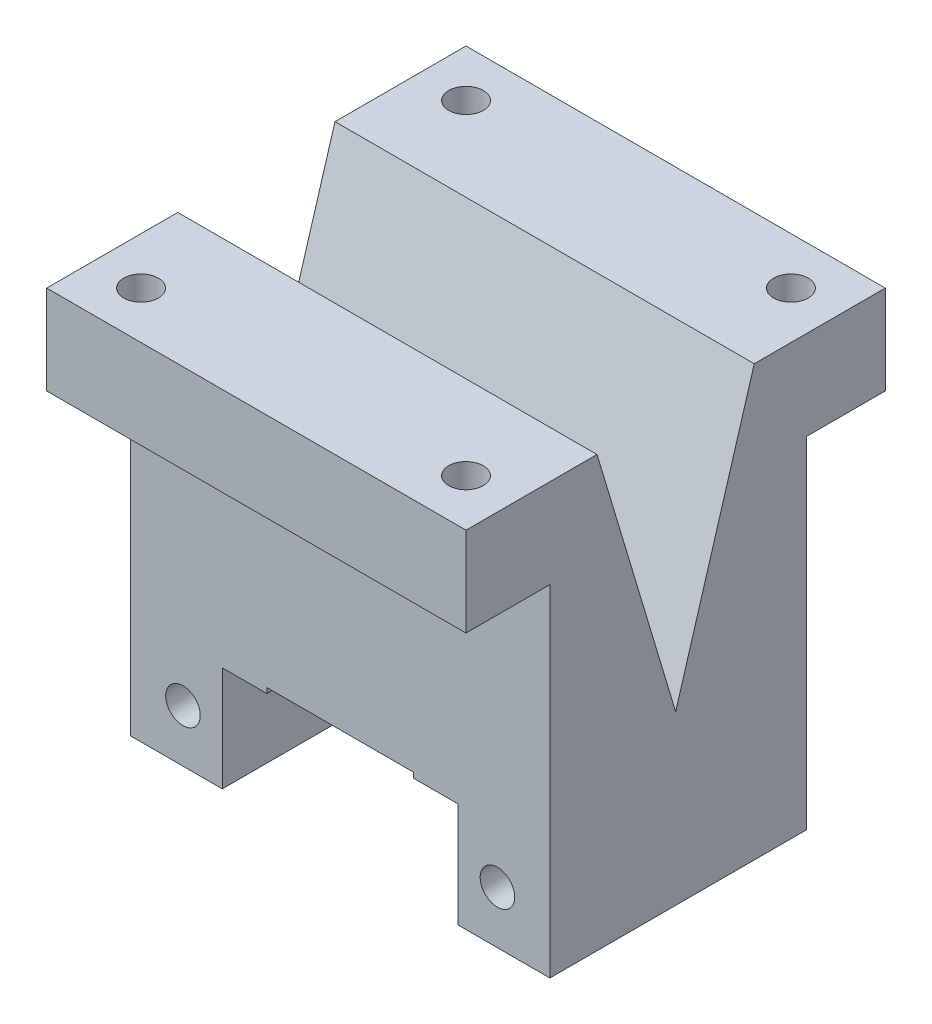
SolidWorks part; units mm, degrees
ref_plane "Front Plane" through (0, 0, 0) normal (0, 0, 1) x (1, 0, 0)
ref_plane "Top Plane" through (0, 0, 0) normal (0, 1, 0) x (1, 0, 0)
ref_plane "Right Plane" through (0, 0, 0) normal (1, 0, 0) x (0, 0, -1)
sketch "Sketch1" plane through (0, 0, 0) normal (0, 1, 0) x (1, 0, 0)
  line L1 (20, 20) -> (-20, 20)
  line L2 (20, 20) -> (20, -20)
  line L3 (20, -20) -> (-20, -20)
  line L4 (-20, 20) -> (-20, -20)
  line L5 (0, -20) -> (0, 20) construction
  line L6 (20, 0) -> (-20, 0) construction
  point P0 (0, 0)
extrude "Boss-Extrude1" add sketch "Sketch1" against normal blind 41
hole_wizard "M4x0.7 Tapped Hole1" positions "Sketch2" profile "Sketch3" tap size "M4x0.7" standard "ANSI Metric" end condition through all
sketch "Sketch2" plane through (0, 0, 0) normal (0, 1, 0) x (1, 0, 0)
  line L1 (-15.5, -15.5) -> (15.5, -15.5)
  line L2 (-15.5, -15.5) -> (-15.5, 15.5)
  line L3 (-15.5, 15.5) -> (15.5, 15.5)
  line L4 (15.5, -15.5) -> (15.5, 15.5)
  line L5 (15.5, 0) -> (0, 0) construction
  line L6 (0, 0) -> (0, -15.5) construction
  point P2 (-15.5, 15.5)
  point P4 (15.5, 15.5)
  point P6 (15.5, -15.5)
  point P8 (-15.5, -15.5)
  dimension "D1" = 31
  dimension "D2" = 31
sketch "Sketch3" plane through (-15.5, 0, -15.5) normal (1, 0, 0) x (0, 0, 1)
  line L0 (0, 0) -> (0, 41)
  line L1 (0, 41) -> (1.65, 41)
  line L2 (1.65, 41) -> (1.65, 0)
  line L5 (1.65, 0) -> (0, 0)
  line L11 (0, -6.35) -> (0, 107.95) construction
  dimension "Thread Major Dia." = 3.3
  dimension "Thru Tap Drill Depth" = 41
sketch "Sketch10" plane through (0, 0, 0) normal (0, 1, 0) x (1, 0, 0)
  line L0 (20, -20) -> (20, 20) construction
  line L1 (-20, -20) -> (20, -20)
  line L2 (-20, -20) -> (-20, 0)
  line L3 (-20, 0) -> (20, 0)
  line L4 (20, -20) -> (20, 0)
sketch "Sketch11" plane through (0, 0, 0) normal (0, 0, 1) x (1, 0, 0)
  line L0 (0, 0) -> (0, -32.5) construction
  line L1 (0, -32.5) -> (11.25, -32.5)
  line L2 (0, -32.5) -> (0, -39.5)
  line L3 (0, -39.5) -> (11.25, -39.5)
  line L4 (11.25, -32.5) -> (11.25, -39.5)
  point P5 (0, 0)
  point P6 (0, 0)
  dimension "D1" = 32.5
  dimension "D2" = 7
  dimension "D3" = 22.5
revolve "Cut-Revolve2" cut sketch "Sketch11" angle 360 about L0
sketch "Sketch12" plane through (0, -41, 0) normal (0, -1, 0) x (1, 0, 0)
  circle A0 centre (0, 0) radius 10
  point P2 (0, 0)
  dimension "D1" = 20
extrude "Cut-Extrude5" cut sketch "Sketch12" against normal up to next
hole_wizard "M4x0.7 Tapped Hole2" positions "Sketch13" profile "Sketch14" tap size "M4x0.7" standard "ANSI Metric" end condition through all
sketch "Sketch13" plane through (0, 0, -20) normal (0, 0, -1) x (-1, 0, 0)
  line L0 (-15, -36) -> (15, -36) construction
  line L3 (0, -36) -> (0, 0) construction
  line L9 (20, -41) -> (-20, -41) construction
  point P8 (15, -36)
  point P10 (-15, -36)
  point P34 (0, 0)
  point P35 (0, 0)
  point P36 (0, 0)
  point P38 (0, 0)
  dimension "D1" = 30
  dimension "D2" = 5
sketch "Sketch14" plane through (-15, -36, -20) normal (1, 0, 0) x (0, 1, 0)
  line L0 (0, 0) -> (0, 40)
  line L1 (0, 40) -> (1.65, 40)
  line L2 (1.65, 40) -> (1.65, 0)
  line L5 (1.65, 0) -> (0, 0)
  line L11 (0, -6.35) -> (0, 107.95) construction
  dimension "Thru Tap Drill Dia." = 3.3
  dimension "Thru Tap Drill Depth" = 40
cosmetic thread "Hole Thread1" parameters "D2"=4
cosmetic thread "Hole Thread2" parameters "D2"=4
sketch "Sketch15" plane through (0, -41, 0) normal (0, -1, 0) x (1, 0, 0)
  line L0 (-20, 0) -> (20, 0) construction
  line L1 (-20, -12.5) -> (20, -12.5)
  line L2 (-20, -12.5) -> (-20, -20)
  line L3 (-20, -20) -> (20, -20)
  line L4 (20, -12.5) -> (20, -20)
  line L5 (-20, -20) -> (-20, 20) construction
  line L6 (-20, -20) -> (-20, 20) construction
  line L7 (20, 20) -> (20, -20) construction
  line L8 (20, 12.5) -> (20, 20)
  line L9 (-20, 20) -> (20, 20)
  line L10 (-20, 12.5) -> (-20, 20)
  line L11 (-20, 12.5) -> (20, 12.5)
  dimension "D1" = 7.5
extrude "Cut-Extrude6" cut sketch "Sketch15" against normal blind 32.5
sketch "Sketch16" plane through (0, 0, 0) normal (0, 0, 1) x (1, 0, 0)
  line L0 (11.25, -32.5) -> (11.25, -39.5)
  line L1 (-11.25, -39.5) -> (-11.25, -32.5)
  line L2 (-11.25, -39.5) -> (-11.25, -32.5)
  line L3 (11.25, -32.5) -> (11.25, -39.5)
  line L4 (-11.25, -32.5) -> (11.25, -32.5)
  line L5 (-11.25, -32.5) -> (11.25, -32.5)
  line L6 (-11.25, -39.5) -> (11.25, -39.5)
  point P4 (11.4669, -39.7)
  point P6 (-10.9624, -39.7)
extrude "Cut-Extrude7" cut sketch "Sketch16" along normal through all
sketch "Sketch17" plane through (0, -41, 0) normal (0, -1, 0) x (1, 0, 0)
  line L0 (-20, 12.5) -> (20, 12.5) construction
  line L1 (-11.25, 0) -> (11.25, 0)
  line L2 (-11.25, 0) -> (-11.25, 12.5)
  line L3 (-11.25, 12.5) -> (11.25, 12.5)
  line L4 (11.25, 0) -> (11.25, 12.5)
  line L5 (0, 12.5) -> (0, 0) construction
  line L6 (-11.25, 6.25) -> (11.25, 6.25) construction
  line L7 (-11.25, 12.5) -> (-11.25, 0) construction
  point P6 (0, 0)
  point P7 (-11.25, 12.5)
  point P392 (0, 6.25)
extrude "Cut-Extrude8" cut sketch "Sketch17" against normal up to next
sketch "Sketch18" plane through (0, -32.5, 0) normal (0, -1, 0) x (1, 0, 0)
  line L0 (-7, 0) -> (-7, 12.5)
  line L1 (11.25, 12.5) -> (-11.25, 12.5) construction
  line L2 (-7, 12.5) -> (7, 12.5)
  line L3 (7, 12.5) -> (7, 0)
  arc A0 (-7, 0) -> (7, 0) centre (0, 0) ccw
  dimension "D1" = 7
extrude "Cut-Extrude9" cut sketch "Sketch18" against normal blind 2
sketch "Sketch19" plane through (-20, 0, 0) normal (-1, 0, 0) x (0, 0, 1)
  line L0 (0, 0) -> (0, -25) construction
  line L1 (-20, 0) -> (20, 0) construction
  line L2 (0, -25) -> (7.5, 0)
  line L3 (7.5, 0) -> (-7.5, 0)
  line L4 (-7.5, 0) -> (0, -25)
  dimension "D1" = 25
  dimension "D2" = 15
extrude "Cut-Extrude10" cut sketch "Sketch19" against normal through all
sketch "Sketch20" plane through (0, 0, 12.5) normal (0, 0, 1) x (1, 0, 0)
  line L1 (-11.25, -41) -> (11.25, -41)
  line L2 (-11.25, -41) -> (-11.25, -31)
  line L3 (-11.25, -31) -> (11.25, -31)
  line L4 (11.25, -41) -> (11.25, -31)
  line L5 (0, -31) -> (0, -41) construction
  line L6 (-11.25, -36) -> (11.25, -36) construction
  point P356 (0, -36)
  dimension "D1" = 10
extrude "Cut-Extrude11" cut sketch "Sketch20" against normal up to surface (12.5 mm away) up to face at (-10.625, -40.25, 0)
sketch "Sketch21" plane through (-20, 0, 0) normal (-1, 0, 0) x (0, 0, 1)
  line L0 (-12.5, -41) -> (12.5, -41) construction
  line L1 (12.5, -8.5) -> (12, -8.5)
  line L2 (12.5, -8.5) -> (12.5, -41)
  line L3 (12.5, -41) -> (12, -41)
  line L4 (12, -8.5) -> (12, -41)
  line L5 (12.25, -41) -> (12.25, -8.5) construction
  line L6 (12.5, -24.75) -> (12, -24.75) construction
  point P432 (12.25, -24.75)
  dimension "D1" = 0.5
extrude "Cut-Extrude12" cut sketch "Sketch21" against normal through all
